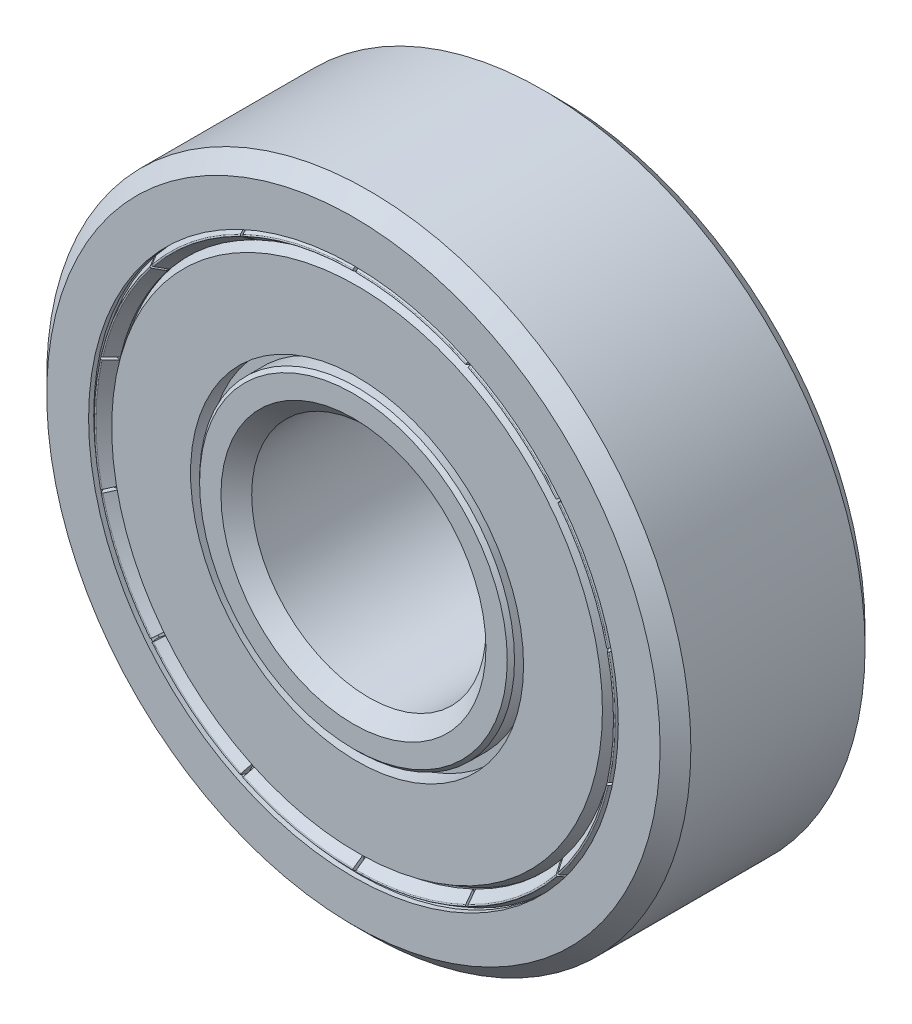
SolidWorks part; units mm, degrees
ref_plane "Front Plane" through (0, 0, 0) normal (0, 0, 1) x (1, 0, 0)
ref_plane "Top Plane" through (0, 0, 0) normal (0, 1, 0) x (1, 0, 0)
ref_plane "Right Plane" through (0, 0, 0) normal (1, 0, 0) x (0, 0, -1)
sketch "Sketch1" plane through (0, 0, 0) normal (0, 0, 1) x (1, 0, 0)
  circle A0 centre (0, 0) radius 4
  circle A1 centre (0, 0) radius 11
  dimension "OD" = 22
  dimension "ID" = 8
sketch "Sketch2" plane through (0, 0, 0) normal (1, 0, 0) x (0, 0, -1)
  line L0 (-3.5, 11) -> (3.5, 11)
  line L1 (-3.5, 4) -> (-3.5, -4) construction
  line L2 (3.5, 11) -> (3.5, -11) construction
  line L3 (-3.5, 0) -> (3.5, 0) construction
  line L6 (0, 11) -> (0, 4) construction
  circle A0 centre (0, 7.5) radius 2.45 construction
  point P8 (0, 11)
  dimension "Approx. Ball Dia." = 4.9
  dimension "Width" = 7
  dimension "For Shaft Diameter" = 8
  dimension "For Housing ID" = 22
sketch "Sketch3" plane through (0, 0, 0) normal (1, 0, 0) x (0, 0, -1)
  line L0 (0, 0) -> (0, 8) construction
  line L1 (-3.5, 4) -> (-3.5, -4) construction
  line L2 (2.975, 11) -> (-2.975, 11)
  line L3 (-2.975, 11) -> (-3.5, 10.475)
  line L4 (-3.5, 10.475) -> (-3.5, 9.046)
  line L5 (-3.5, 9.046) -> (-3.325, 9.046)
  line L6 (-3.325, 9.046) -> (-3.325, 9.498)
  line L7 (-3.325, 9.498) -> (-3.2013, 9.6218)
  line L8 (-3.2013, 9.6218) -> (-1.225, 9.6218)
  line L10 (-3.5, 11) -> (3.5, 11) construction
  line L12 (-3.325, 9.498) -> (-3.325, 9.95) construction
  line L13 (3.2013, 9.6218) -> (1.225, 9.6218)
  line L14 (3.325, 9.498) -> (3.2013, 9.6218)
  line L15 (3.325, 9.046) -> (3.325, 9.498)
  line L16 (3.5, 9.046) -> (3.325, 9.046)
  line L17 (3.5, 10.475) -> (3.5, 9.046)
  line L18 (2.975, 11) -> (3.5, 10.475)
  line L19 (2.975, 4) -> (-2.975, 4)
  line L20 (-2.975, 4) -> (-3.5, 4.525)
  line L21 (-3.5, 4.525) -> (-3.5, 5.2545)
  line L22 (-3.5, 5.2545) -> (-3.3763, 5.3782)
  line L23 (-3.3763, 5.3782) -> (-1.225, 5.3782)
  line L25 (3.3763, 5.3782) -> (1.225, 5.3782)
  line L26 (3.5, 5.2545) -> (3.3763, 5.3782)
  line L27 (3.5, 4.525) -> (3.5, 5.2545)
  line L28 (2.975, 4) -> (3.5, 4.525)
  circle A2 centre (0, 7.5) radius 2.45 construction
  arc A3 (-1.225, 9.6218) -> (1.225, 9.6218) centre (0, 7.5) cw
  arc A4 (-1.225, 5.3782) -> (1.225, 5.3782) centre (0, 7.5) ccw
  point P5 (0, 9.95)
  point P31 (0, 11)
  point P37 (0, 4)
  dimension "D1" = 45
  dimension "D2" = 0.175
  dimension "D3" = 2.45
  dimension "D4" = 0.525
revolve "Revolve1" add sketch "Sketch3" angle 360 about L3
sketch "Sketch4" plane through (0, 0, 0) normal (1, 0, 0) x (0, 0, -1)
  line L0 (0, 9.95) -> (0, 5.05)
  line L1 (0, 11) -> (0, 4) construction
  circle A0 centre (0, 7.5) radius 2.45 construction
  arc A1 (0, 5.05) -> (0, 9.95) centre (0, 7.5) cw
revolve "Revolve2" add sketch "Sketch4" angle 360 about L6
pattern_circular "CirPattern1" count 7 over 360 about axis through (0, 0, 0) along (0, 0, 1) of bodies 106
sketch "Sketch5" plane through (0, 0, 0) normal (1, 0, 0) x (0, 0, -1)
  line L0 (-2.45, 7.5) -> (-2.45, 5.3782) construction
  line L1 (-3.3763, 5.3782) -> (-1.225, 5.3782) construction
  line L3 (-2.45, 5.3782) -> (-2.7588, 5.3782)
  line L4 (-2.7588, 5.3782) -> (-2.7588, 5.687)
  line L5 (-2.7588, 5.687) -> (-3.3763, 5.687)
  line L6 (-3.3763, 5.687) -> (-3.3763, 8.3808)
  line L7 (-3.3763, 8.3808) -> (-2.7588, 8.7373)
  line L8 (-2.7588, 8.7373) -> (-2.45, 8.7373)
  line L9 (-2.45, 8.7373) -> (-2.45, 5.3782)
  line L10 (0, 7.5) -> (0, 11) construction
  line L11 (2.7588, 8.7373) -> (2.45, 8.7373)
  line L12 (3.3763, 8.3808) -> (2.7588, 8.7373)
  line L13 (3.3763, 5.687) -> (3.3763, 8.3808)
  line L14 (2.7588, 5.687) -> (3.3763, 5.687)
  line L15 (2.7588, 5.3782) -> (2.7588, 5.687)
  line L16 (2.45, 5.3782) -> (2.7588, 5.3782)
  line L17 (2.45, 8.7373) -> (2.45, 5.3782)
  line L18 (-3.3763, 8.3808) -> (-3.0675, 8.3808) construction
  line L19 (-3.0675, 8.3808) -> (-2.7588, 8.3808) construction
  line L20 (-2.7588, 8.3808) -> (-2.45, 8.3808) construction
  line L21 (-2.7588, 8.7373) -> (-2.7588, 9.046) construction
  circle A0 centre (0, 7.5) radius 2.45 construction
  dimension "D1" = 30
revolve "Revolve3" add sketch "Sketch5" angle 360 about L3
sketch "Sketch6" plane through (0, 0, 0) normal (1, 0, 0) x (0, 0, -1)
  line L0 (-2.9945, 9.046) -> (-3.1938, 9.046)
  line L1 (-3.1938, 9.046) -> (-3.5, 8.8692)
  line L2 (-3.5, 8.8692) -> (-3.0995, 8.5888)
  line L4 (-3.3763, 8.3808) -> (-2.7588, 8.7373) construction
  line L5 (-2.9945, 8.6012) -> (-2.9945, 9.046)
  line L6 (-3.5, 9.046) -> (-3.325, 9.046) construction
  line L7 (-3.0995, 8.5888) -> (-3.0645, 8.5888)
  line L8 (-3.0645, 8.5888) -> (-2.9945, 8.6012)
  line L9 (-3.5, 10.475) -> (-3.5, -10.475) construction
  line L11 (-3.0645, 8.5888) -> (-3.0295, 8.5888) construction
  line L12 (-3.0295, 8.5888) -> (-2.9945, 8.5888) construction
  point P27 (-3.0941, 9.046)
  dimension "D1" = 30
  dimension "D3" = 10
  dimension "D2" = 35
  dimension "D4" = 0.035
  dimension "D5" = 0.3062
revolve "Revolve4" add sketch "Sketch6" angle 360 about L3
fillet "Fillet1" radius 0.035 1 edges at (8.8692, 0, 3.5)
sketch "Sketch7" plane through (0, 0, 0) normal (0, 0, 1) x (1, 0, 0)
  line L0 (-0.05, 9.046) -> (-0.05, 9.146)
  line L1 (-0.05, 9.046) -> (0.05, 9.046) construction
  line L2 (-0.05, 9.046) -> (-0.05, 8.5888)
  line L3 (-0.05, 8.5888) -> (0.05, 8.5888) construction
  line L4 (0.05, 9.046) -> (0.05, 8.5888)
  line L5 (-0.05, 9.146) -> (0.05, 9.146)
  line L6 (0.05, 9.146) -> (0.05, 9.046)
  line L7 (-0.05, 8.5888) -> (-0.05, 8.4888)
  line L8 (-0.05, 8.4888) -> (0.05, 8.4888)
  line L9 (0.05, 8.4888) -> (0.05, 8.5888)
  dimension "D1" = 0.1
extrude "Cut-Extrude1" cut sketch "Sketch7" along normal through all from vertex at 3.0941 starting at point (0, 9.046, 3.0941)
pattern_circular "CirPattern2" count 14 over 360 about axis through (0, 0, 3.5) along (0, 0, -1) of "Cut-Extrude1"
mirror "Mirror1" about plane through (0, 0, 0) normal (0, 0, 1) of bodies 120
equation "\"Approx. Ball Dia.@Sketch2\"=( \"OD@Sketch1\" - \"ID@Sketch1\" )  * .5 * .7"
equation "\"D2@Sketch3\"=\"Width@Sketch2\"*.025"
equation "\"D3@Sketch3\"=\"Approx. Ball Dia.@Sketch2\"*.5"
equation "\"D4@Sketch3\"=\"Width@Sketch2\"*.075"
equation "\"Approx No of Balls\"= ( pi * \"OD@Sketch1\" ) * .5 / \"Approx. Ball Dia.@Sketch2\""
equation "\"D1@CirPattern1\"=\"Approx No of Balls\""
equation "\"D4@Sketch6\"=\"D2@Sketch3\"*.2"
equation "\"D1@CirPattern2\"=\"Approx No of Balls\"*2"
equation "\"D5@Sketch6\"=\"D2@Sketch3\"*1.75"
equation "\"D1@Fillet1\"=\"d4@sketch6\""
